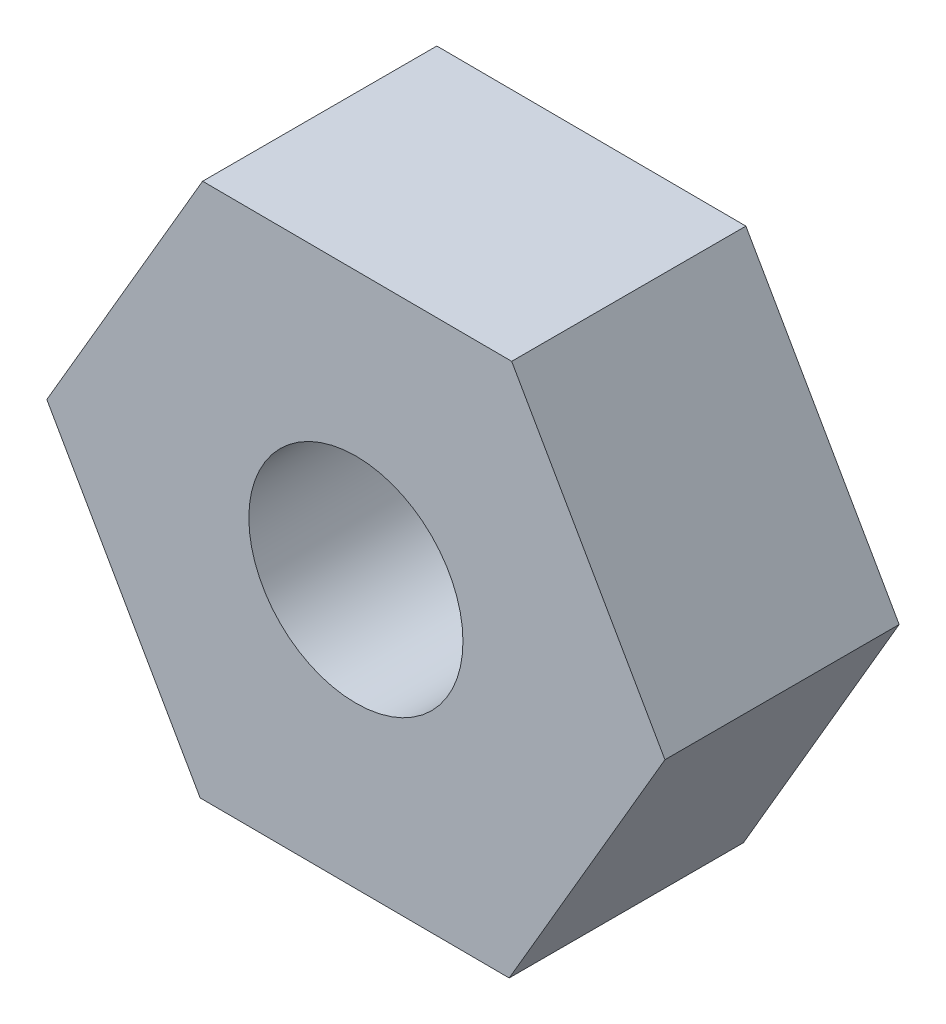
SolidWorks part; units mm, degrees
ref_plane "前视基准面" through (0, 0, 0) normal (0, 0, 1) x (1, 0, 0)
ref_plane "上视基准面" through (0, 0, 0) normal (0, 1, 0) x (1, 0, 0)
ref_plane "右视基准面" through (0, 0, 0) normal (1, 0, 0) x (0, 0, -1)
sketch "草图1" plane through (0, 0, 0) normal (0, 0, 1) x (1, 0, 0)
  line L1 (-2.2907, 4.0107) -> (-4.6188, 0.0216)
  line L2 (-4.6188, 0.0216) -> (-2.328, -3.9892)
  line L3 (-2.328, -3.9892) -> (2.2907, -4.0107)
  line L4 (2.2907, -4.0107) -> (4.6188, -0.0216)
  line L5 (4.6188, -0.0216) -> (2.328, 3.9892)
  line L6 (2.328, 3.9892) -> (-2.2907, 4.0107)
  circle A0 centre (0, 0) radius 4 construction
  circle A1 centre (0, 0) radius 1.6
  dimension "D1" = 3.2
  dimension "D2" = 8
extrude "凸台-拉伸1" add sketch "草图1" along normal blind 3.5
